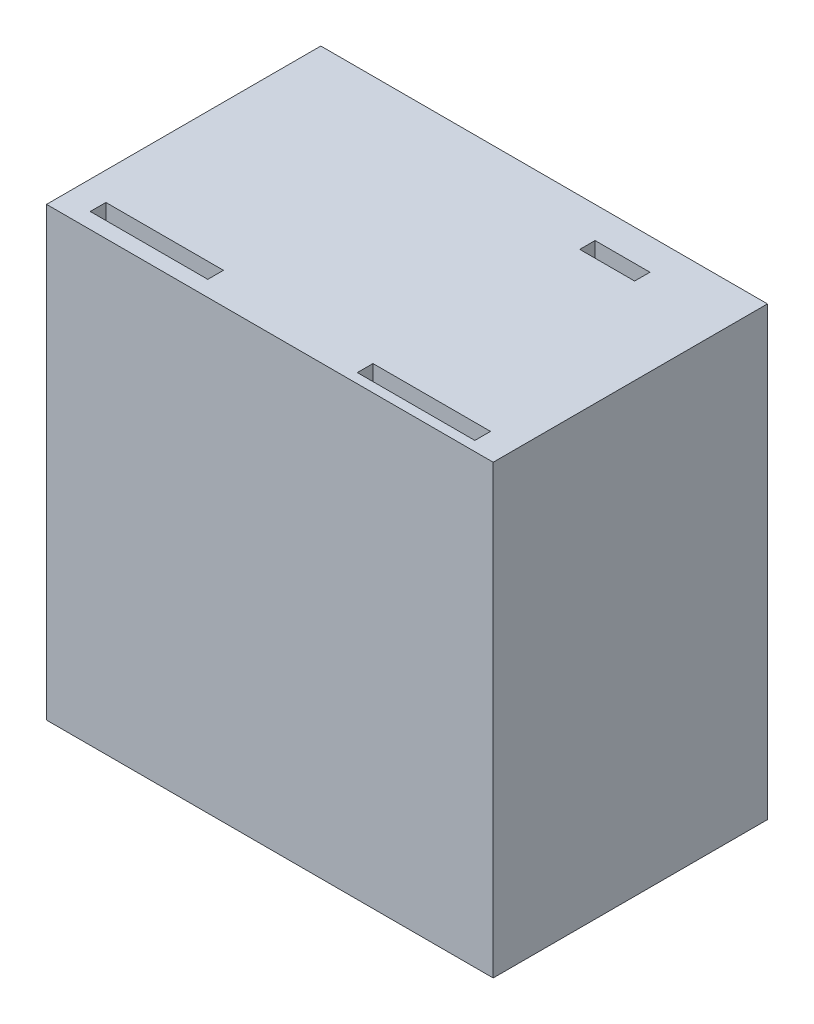
SolidWorks part; units mm, degrees
ref_plane "Front Plane" through (0, 0, 0) normal (0, 0, 1) x (1, 0, 0)
ref_plane "Top Plane" through (0, 0, 0) normal (0, 1, 0) x (1, 0, 0)
ref_plane "Right Plane" through (0, 0, 0) normal (1, 0, 0) x (0, 0, -1)
sketch "Sketch2" plane through (0, 0, 0) normal (0, 0, 1) x (1, 0, 0)
  line L5 (-34.233, 27.7621) -> (22.767, 27.7621)
  line L6 (-34.233, 27.7621) -> (-34.233, -29.2379)
  line L7 (-34.233, -29.2379) -> (22.767, -29.2379)
  line L8 (22.767, 27.7621) -> (22.767, -29.2379)
  dimension "D1" = 57
  dimension "D2" = 57
extrude "Boss-Extrude1" add sketch "Sketch2" along normal blind 35
sketch "Sketch3" plane through (0, 27.7621, 0) normal (0, 1, 0) x (1, 0, 0)
  line L0 (22.767, -35) -> (-34.233, -35) construction
  line L1 (-30.6564, -31) -> (-15.6564, -31)
  line L2 (-30.6564, -31) -> (-30.6564, -33)
  line L3 (-30.6564, -33) -> (-15.6564, -33)
  line L4 (-15.6564, -31) -> (-15.6564, -33)
  line L5 (4.187, -31.7612) -> (19.187, -31.7612)
  line L6 (4.187, -31.7612) -> (4.187, -33.7612)
  line L7 (4.187, -33.7612) -> (19.187, -33.7612)
  line L8 (19.187, -31.7612) -> (19.187, -33.7612)
  line L9 (-34.233, -35) -> (-34.233, 0) construction
  line L10 (22.767, -35) -> (22.767, 0) construction
  line L11 (22.767, 0) -> (-34.233, 0) construction
  dimension "D1" = 2
  dimension "D2" = 1.2388
  dimension "D3" = 15
  dimension "D4" = 3.5766
  dimension "D5" = 3.58
  dimension "D6" = 31
extrude "Cut-Extrude1" cut sketch "Sketch3" against normal blind 60
sketch "Sketch4" plane through (0, 0, 0) normal (0, 0, -1) x (-1, 0, 0)
  line L0 (-22.767, -29.2379) -> (-22.767, 27.7621) construction
  line L1 (-15.267, 20.2621) -> (26.733, 20.2621)
  line L2 (-15.267, 20.2621) -> (-15.267, -21.7379)
  line L3 (-15.267, -21.7379) -> (26.733, -21.7379)
  line L4 (26.733, 20.2621) -> (26.733, -21.7379)
  line L5 (34.233, -29.2379) -> (-22.767, -29.2379) construction
  dimension "D1" = 42
  dimension "D2" = 42
  dimension "D3" = 7.5
  dimension "D4" = 7.5
extrude "Cut-Extrude2" cut sketch "Sketch4" against normal blind 28
sketch "Sketch5" plane through (0, -21.7379, 0) normal (0, 1, 0) x (1, 0, 0)
  line L0 (-26.733, -28) -> (-26.733, 0) construction
  line L3 (15.267, 0) -> (-26.733, 0) construction
  line L5 (2.767, -11) -> (2.767, 0)
  line L6 (2.767, 0) -> (-14.233, 0)
  line L7 (-14.233, 0) -> (-14.233, -11)
  arc A0 (-14.233, -11) -> (2.767, -11) centre (-5.733, -11) ccw
  dimension "D3" = 8.5
  dimension "D1" = 21
  dimension "D2" = 11
extrude "Cut-Extrude4" cut sketch "Sketch5" against normal blind 5
sketch "Sketch7" plane through (-26.733, 0, 0) normal (1, 0, 0) x (0, 0, -1)
  line L0 (-28, -21.7379) -> (0, -21.7379) construction
  line L2 (0, -21.7379) -> (0, 20.2621) construction
  line L3 (-11, -9.2379) -> (0, -9.2379)
  line L4 (0, -9.2379) -> (0, 7.7621)
  line L8 (0, 7.7621) -> (-11, 7.7621)
  arc A1 (-11, 7.7621) -> (-11, -9.2379) centre (-11, -0.7379) ccw
  dimension "D3" = 8.5
  dimension "D1" = 21
  dimension "D2" = 11
extrude "Cut-Extrude5" cut sketch "Sketch7" against normal blind 10
sketch "Sketch8" plane through (0, -26.7379, 0) normal (0, 1, 0) x (1, 0, 0)
  line L1 (-14.233, 0) -> (2.767, 0)
  line L4 (2.767, 0) -> (2.767, -11)
  line L5 (-14.233, 0) -> (-14.233, -11)
  arc A0 (2.767, -11) -> (-14.233, -11) centre (-5.733, -11) cw
extrude "Cut-Extrude6" cut sketch "Sketch8" against normal blind 5
sketch "Sketch13" plane through (0, 27.7621, 0) normal (0, 1, 0) x (1, 0, 0)
  line L1 (4.767, -4) -> (11.767, -4)
  line L2 (4.767, -4) -> (4.767, -5.9526)
  line L3 (4.767, -5.9526) -> (11.767, -5.9526)
  line L4 (11.767, -4) -> (11.767, -5.9526)
  line L6 (22.767, -35) -> (22.767, 0) construction
  line L7 (-34.233, -35) -> (-34.233, 0) construction
  line L8 (22.767, 0) -> (-34.233, 0) construction
  dimension "D1" = 11
  dimension "D2" = 39
  dimension "D3" = 4
extrude "Cut-Extrude8" cut sketch "Sketch13" against normal blind 12
